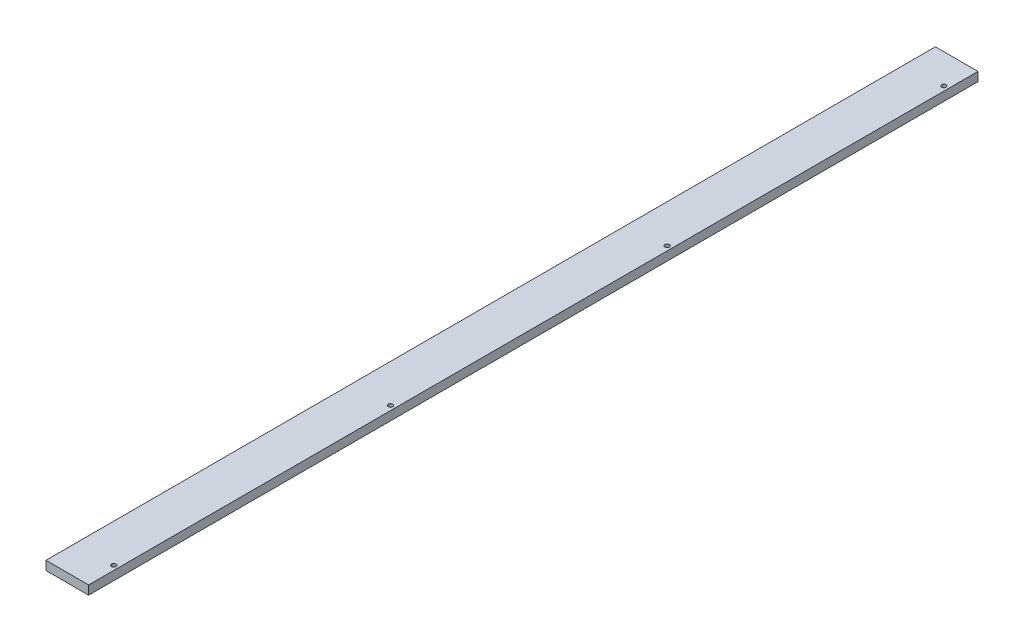
SolidWorks part; units mm, degrees
ref_plane "Front Plane" through (0, 0, 0) normal (0, 0, 1) x (1, 0, 0)
ref_plane "Top Plane" through (0, 0, 0) normal (0, 1, 0) x (1, 0, 0)
ref_plane "Right Plane" through (0, 0, 0) normal (1, 0, 0) x (0, 0, -1)
sketch "Sketch1" plane through (0, 0, 0) normal (0, 1, 0) x (1, 0, 0)
  line L1 (0, 0) -> (62, 0)
  line L2 (0, 0) -> (0, 1200)
  line L3 (0, 1200) -> (62, 1200)
  line L4 (62, 0) -> (62, 1200)
  dimension "D1" = 1200
  dimension "D2" = 62
extrude "Boss-Extrude1" add sketch "Sketch1" along normal blind 12
sketch "Sketch2" plane through (0, 12, 0) normal (0, 1, 0) x (1, 0, 0)
  line L0 (62, 0) -> (62, 1200) construction
  line L1 (0, 0) -> (62, 0) construction
  line L2 (62, 1200) -> (0, 1200) construction
  circle A0 centre (56, 40) radius 3
  circle A1 centre (56, 413.3333) radius 3
  circle A2 centre (56, 786.6667) radius 3
  circle A3 centre (56, 1160) radius 3
  dimension "D1" = 6
  dimension "D2" = 6
  dimension "D3" = 40
  dimension "D5" = 40
  dimension "D4" = 4
extrude "Cut-Extrude1" cut sketch "Sketch2" against normal blind 22
sketch "Sketch3" plane through (0, 12, 0) normal (0, 1, 0) x (1, 0, 0)
  line L0 (0, 1200) -> (0, 0) construction
  line L1 (4.5, 0) -> (-4.2539, 0)
  line L2 (4.5, 0) -> (4.5, 1524)
  line L3 (4.5, 1524) -> (-4.2539, 1524)
  line L4 (-4.2539, 0) -> (-4.2539, 1524)
  line L5 (0, 0) -> (62, 0) construction
  dimension "D1" = 4.5
  dimension "D2" = 1524
extrude "Cut-Extrude2" cut sketch "Sketch3" against normal blind 20
